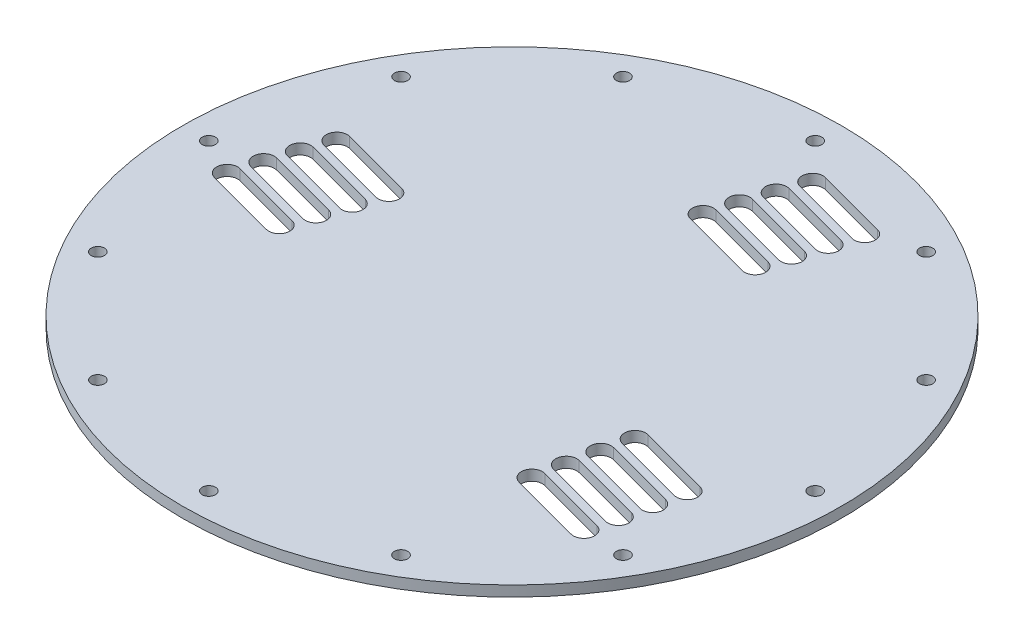
SolidWorks part; units mm, degrees
ref_plane "Front Plane" through (0, 0, 0) normal (0, 0, 1) x (1, 0, 0)
ref_plane "Top Plane" through (0, 0, 0) normal (0, 1, 0) x (1, 0, 0)
ref_plane "Right Plane" through (0, 0, 0) normal (1, 0, 0) x (0, 0, -1)
sketch "Sketch1" plane through (0, 0, 0) normal (0, 1, 0) x (1, 0, 0)
  line L0 (-99.5929, 57.5) -> (-115, 0) construction
  line L3 (11.8238, 44.127) -> (29.9849, 111.9051) construction
  line L12 (0, 0) -> (0, 40.9268) construction
  line L13 (-90.768, 24.3212) -> (-63.7801, 17.0898) construction
  line L14 (-89.7328, 28.1849) -> (-62.7448, 20.9535)
  line L15 (-91.8033, 20.4575) -> (-64.8154, 13.2261)
  line L16 (-94.1672, 13.8596) -> (-67.1793, 6.6282) construction
  line L17 (-93.132, 17.7233) -> (-66.144, 10.4919)
  line L18 (-95.2025, 9.9959) -> (-68.2145, 2.7645)
  line L19 (-97.5664, 3.398) -> (-70.5785, -3.8334) construction
  line L20 (-96.5311, 7.2617) -> (-69.5432, 0.0303)
  line L21 (-98.6017, -0.4657) -> (-71.6137, -7.6971)
  line L22 (-100.9656, -7.0636) -> (-73.9776, -14.295) construction
  line L23 (-99.9303, -3.1999) -> (-72.9424, -10.4313)
  line L24 (-102.0009, -10.9273) -> (-75.0129, -18.1587)
  line L25 (0, 0) -> (11.8238, 44.127) construction
  line L26 (90.768, -24.3212) -> (63.7801, -17.0898) construction
  line L27 (91.8033, -20.4575) -> (64.8154, -13.2261)
  line L28 (89.7328, -28.1849) -> (62.7448, -20.9535)
  line L29 (88.481, -35.0808) -> (61.4931, -27.8494) construction
  line L30 (89.5163, -31.2171) -> (62.5283, -23.9857)
  line L31 (87.4457, -38.9446) -> (60.4578, -31.7131)
  line L32 (86.194, -45.8405) -> (59.206, -38.6091) construction
  line L33 (87.2293, -41.9768) -> (60.2413, -34.7454)
  line L34 (85.1587, -49.7042) -> (58.1707, -42.4728)
  line L35 (83.907, -56.6001) -> (56.919, -49.3687) construction
  line L36 (84.9422, -52.7364) -> (57.9543, -45.505)
  line L37 (82.8717, -60.4638) -> (55.8837, -53.2324)
  line L38 (115, 0) -> (99.5929, -57.5) construction
  line L39 (12.9864, 101.0368) -> (39.9743, 93.8054) construction
  line L40 (14.0217, 104.9005) -> (41.0096, 97.6691)
  line L41 (11.9511, 97.1731) -> (38.9391, 89.9417)
  line L42 (9.5872, 90.5752) -> (36.5752, 83.3438) construction
  line L43 (10.6225, 94.4389) -> (37.6104, 87.2075)
  line L44 (8.5519, 86.7115) -> (35.5399, 79.4801)
  line L45 (6.188, 80.1136) -> (33.176, 72.8822) construction
  line L46 (7.2233, 83.9773) -> (34.2112, 76.7459)
  line L47 (5.1527, 76.2499) -> (32.1407, 69.0185)
  line L48 (2.7888, 69.652) -> (29.7768, 62.4206) construction
  line L49 (3.8241, 73.5157) -> (30.8121, 66.2843)
  line L50 (1.7535, 65.7883) -> (28.7415, 58.5569)
  circle A0 centre (-115, 0) radius 2.5
  circle A1 centre (-99.5929, 57.5) radius 2.5
  circle A2 centre (-57.5, 99.5929) radius 2.5
  circle A3 centre (0, 115) radius 2.5
  circle A4 centre (57.5, 99.5929) radius 2.5
  circle A5 centre (99.5929, 57.5) radius 2.5
  circle A6 centre (115, 0) radius 2.5
  circle A7 centre (99.5929, -57.5) radius 2.5
  circle A8 centre (57.5, -99.5929) radius 2.5
  circle A9 centre (0, -115) radius 2.5
  circle A10 centre (-57.5, -99.5929) radius 2.5
  circle A11 centre (-99.5929, -57.5) radius 2.5
  circle A13 centre (0, 0) radius 125
  arc A14 (-89.7328, 28.1849) -> (-91.8033, 20.4575) centre (-90.768, 24.3212) ccw
  arc A15 (-64.8154, 13.2261) -> (-62.7448, 20.9535) centre (-63.7801, 17.0898) ccw
  arc A16 (-93.132, 17.7233) -> (-95.2025, 9.9959) centre (-94.1672, 13.8596) ccw
  arc A17 (-68.2145, 2.7645) -> (-66.144, 10.4919) centre (-67.1793, 6.6282) ccw
  arc A18 (-96.5311, 7.2617) -> (-98.6017, -0.4657) centre (-97.5664, 3.398) ccw
  arc A19 (-71.6137, -7.6971) -> (-69.5432, 0.0303) centre (-70.5785, -3.8334) ccw
  arc A20 (-99.9303, -3.1999) -> (-102.0009, -10.9273) centre (-100.9656, -7.0636) ccw
  arc A21 (-75.0129, -18.1587) -> (-72.9424, -10.4313) centre (-73.9776, -14.295) ccw
  arc A22 (91.8033, -20.4575) -> (89.7328, -28.1849) centre (90.768, -24.3212) cw
  arc A23 (62.7448, -20.9535) -> (64.8154, -13.2261) centre (63.7801, -17.0898) cw
  arc A24 (89.5163, -31.2171) -> (87.4457, -38.9446) centre (88.481, -35.0808) cw
  arc A25 (60.4578, -31.7131) -> (62.5283, -23.9857) centre (61.4931, -27.8494) cw
  arc A26 (87.2293, -41.9768) -> (85.1587, -49.7042) centre (86.194, -45.8405) cw
  arc A27 (58.1707, -42.4728) -> (60.2413, -34.7454) centre (59.206, -38.6091) cw
  arc A28 (84.9422, -52.7364) -> (82.8717, -60.4638) centre (83.907, -56.6001) cw
  arc A29 (55.8837, -53.2324) -> (57.9543, -45.505) centre (56.919, -49.3687) cw
  arc A30 (14.0217, 104.9005) -> (11.9511, 97.1731) centre (12.9864, 101.0368) ccw
  arc A31 (38.9391, 89.9417) -> (41.0096, 97.6691) centre (39.9743, 93.8054) ccw
  arc A32 (10.6225, 94.4389) -> (8.5519, 86.7115) centre (9.5872, 90.5752) ccw
  arc A33 (35.5399, 79.4801) -> (37.6104, 87.2075) centre (36.5752, 83.3438) ccw
  arc A34 (7.2233, 83.9773) -> (5.1527, 76.2499) centre (6.188, 80.1136) ccw
  arc A35 (32.1407, 69.0185) -> (34.2112, 76.7459) centre (33.176, 72.8822) ccw
  arc A36 (3.8241, 73.5157) -> (1.7535, 65.7883) centre (2.7888, 69.652) ccw
  arc A37 (28.7415, 58.5569) -> (30.8121, 66.2843) centre (29.7768, 62.4206) ccw
  point P28 (0, 0)
  point P31 (-77.2741, 20.7055)
  point P40 (-80.6733, 10.2439)
  point P47 (-84.0724, -0.2177)
  point P54 (-87.4716, -10.6793)
  point P61 (77.2741, -20.7055)
  point P68 (74.987, -31.4651)
  point P75 (72.7, -42.2248)
  point P82 (70.413, -52.9844)
  point P89 (26.4804, 97.4211)
  point P96 (23.0812, 86.9595)
  point P103 (19.682, 76.4979)
  point P110 (16.2828, 66.0363)
  dimension "D1" = 27.94
  dimension "D2" = 5
  dimension "D4" = 250
  dimension "D5" = 80
  dimension "D6" = 8
  dimension "D9" = 8
  dimension "D7" = 4
  dimension "D8" = 27.94
  dimension "D3" = 12
extrude "Boss-Extrude1" add sketch "Sketch1" along normal blind 4
